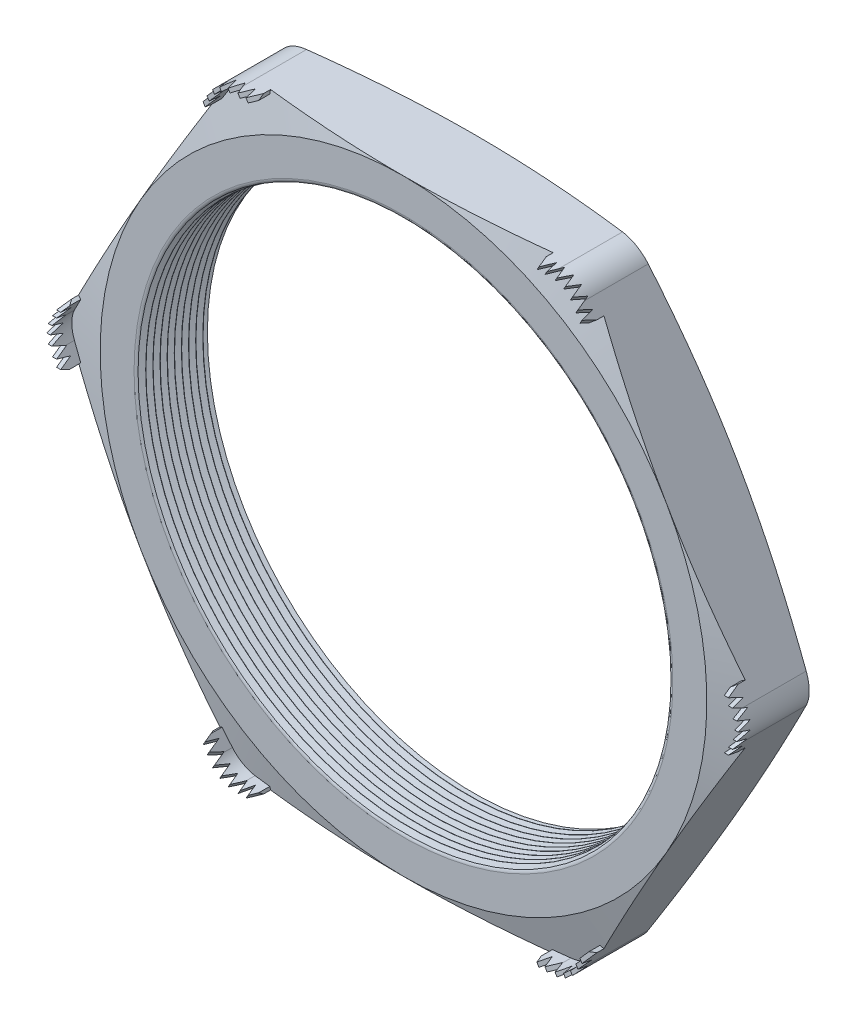
SolidWorks part; units mm, degrees
ref_plane "Front Plane" through (0, 0, 0) normal (0, 0, 1) x (1, 0, 0)
ref_plane "Top Plane" through (0, 0, 0) normal (0, 1, 0) x (1, 0, 0)
ref_plane "Right Plane" through (0, 0, 0) normal (1, 0, 0) x (0, 0, -1)
sketch "Sketch1" plane through (0, 0, 0) normal (0, 0, 1) x (1, 0, 0)
  line L1 (-14.958, 0) -> (-7.479, -12.954)
  line L2 (-7.479, -12.954) -> (7.479, -12.954)
  line L3 (7.479, -12.954) -> (14.958, 0)
  line L4 (14.958, 0) -> (7.479, 12.954)
  line L5 (7.479, 12.954) -> (-7.479, 12.954)
  line L6 (-7.479, 12.954) -> (-14.958, 0)
  circle A0 centre (0, 0) radius 12.954 construction
  circle A1 centre (0, 0) radius 11.303
  dimension "TS" = 22.606
  dimension "H" = 25.908
extrude "Extrude1" add sketch "Sketch1" along normal blind 3.048
fillet "Fillet1" radius 1.27 6 edges at (-7.479, 12.954, 1.524) (-14.958, 0, 1.524) (-7.479, -12.954, 1.524) (7.479, -12.954, 1.524) (14.958, 0, 1.524) (7.479, 12.954, 1.524)
sketch "Sketch2" plane through (0, 0, 3.048) normal (0, 0, 1) x (1, 0, 0)
  line L0 (-6.7458, 12.954) -> (-6.0346, 12.954)
  line L1 (6.7458, 12.954) -> (-6.7458, 12.954) construction
  line L2 (-7.8456, 12.319) -> (-8.2012, 11.7031)
  line L3 (-7.8456, 12.319) -> (-14.5914, 0.635) construction
  line L4 (-6.7458, 12.8016) -> (-6.0346, 12.8016)
  line L5 (-7.7136, 12.2428) -> (-8.0692, 11.6269)
  line L6 (-8.2012, 11.7031) -> (-8.0692, 11.6269)
  line L7 (-6.0346, 12.954) -> (-6.0346, 12.8016)
  arc A0 (-6.7458, 12.8016) -> (-7.7136, 12.2428) centre (-6.7458, 11.684) ccw
  arc A1 (-6.7458, 12.954) -> (-7.8456, 12.319) centre (-6.7458, 11.684) ccw construction
  arc A4 (-6.7458, 12.954) -> (-7.8456, 12.319) centre (-6.7458, 11.684) ccw
  dimension "D1" = 0.7112
  dimension "D2" = 0.7112
  dimension "OFFSET" = 0.1524
fillet "Fillet3" radius 0.2032 2 edges at (11.303, 0, 0) (11.303, 0, 3.048)
sketch "Sketch3" plane through (0, 0, 0) normal (0, 1, 0) x (1, 0, 0)
  line L0 (-11.303, -3.048) -> (-11.303, -2.7547)
  line L2 (-11.303, -2.7547) -> (-11.557, -2.9014)
  line L3 (-11.557, -2.9014) -> (-11.303, -3.048)
  line L4 (-11.303, -0.2032) -> (-11.303, -2.8448) construction
  line L5 (-7.8456, -3.048) -> (-14.5914, -3.048) construction
  dimension "D1" = 60
  dimension "D2" = 60
  dimension "D3" = 0.254
revolve "Cut-Revolve1" cut sketch "Sketch3" angle 360 about axis through (0, 0, 3.048) along (0, 0, -1)
pattern_linear "LPattern1" count 10 spacing 0.3048 along (0, 0, -1) of "Cut-Revolve1"
sketch "Sketch4" plane through (0, 0, 0) normal (0, 0, -1) x (-1, 0, 0)
  line L0 (-14.5914, 0.635) -> (-7.8456, 12.319) construction
  circle A0 centre (0, 0) radius 12.954
extrude "Cut-Extrude1" cut sketch "Sketch4" against normal through all draft 75 flip side to cut
sketch "Sketch5" plane through (0, 0, 3.048) normal (0, 0, 1) x (1, 0, 0)
  line L0 (6.7458, 12.954) -> (-6.7458, 12.954) construction
  circle A0 centre (0, 0) radius 12.954
extrude "Cut-Extrude2" cut sketch "Sketch5" against normal through all draft 75 flip side to cut
extrude "Extrude2" add sketch "Sketch2" along normal blind 1.27 and the other way up to next
ref_plane "Plane1" through (-7.0519, 12.2142, 0) normal (0.5, -0.866, 0) x (0.866, 0.5, 0)
sketch "Sketch7" plane through (-7.0519, 12.2142, 0) normal (0.5, -0.866, 0) x (0.866, 0.5, 0)
  line L0 (-1.2509, 2.9845) -> (-1.0604, 3.5179)
  line L1 (-1.2509, 2.6899) -> (-1.2509, 4.318) construction
  line L2 (0, 1.3136) -> (0, 4.0135) construction
  line L4 (-1.0604, 3.5179) -> (-0.8699, 2.9845)
  line L5 (-0.381, 3.5179) -> (-0.1905, 2.9845)
  line L6 (-0.762, 3.5179) -> (-0.5715, 2.9845)
  line L7 (-0.1905, 2.9845) -> (0, 3.5179)
  line L8 (0, 3.5179) -> (0.1905, 2.9845)
  line L10 (0.381, 3.5179) -> (0.5715, 2.9845)
  line L11 (0.762, 3.5179) -> (0.9525, 2.9845)
  line L12 (-0.8699, 2.9845) -> (-0.762, 3.5179)
  line L13 (-0.5715, 2.9845) -> (-0.381, 3.5179)
  line L14 (0.1905, 2.9845) -> (0.381, 3.5179)
  line L15 (1.0604, 3.5179) -> (1.2509, 2.9845)
  line L16 (1.2509, 2.6899) -> (1.2509, 4.318) construction
  line L17 (-1.2509, 2.9845) -> (-1.2509, 4.318)
  line L19 (-1.2509, 4.318) -> (1.2509, 4.318)
  line L20 (1.2509, 4.318) -> (1.2509, 2.9845)
  line L23 (0.5715, 2.9845) -> (0.762, 3.5179)
  line L25 (0.9525, 2.9845) -> (1.0604, 3.5179)
  dimension "D1" = 1.3335
  dimension "D2" = 0.8001
  dimension "D3" = 0.1905
extrude "Cut-Extrude4" cut sketch "Sketch7" against normal through all
pattern_circular "CirPattern1" count 6 over 360 about axis through (0, 0, 0) along (0, 0, 1) of "Extrude2"
pattern_circular "CirPattern2" count 6 over 360 about axis through (0, 0, 0) along (0, 0, 1) of "Cut-Extrude4"
